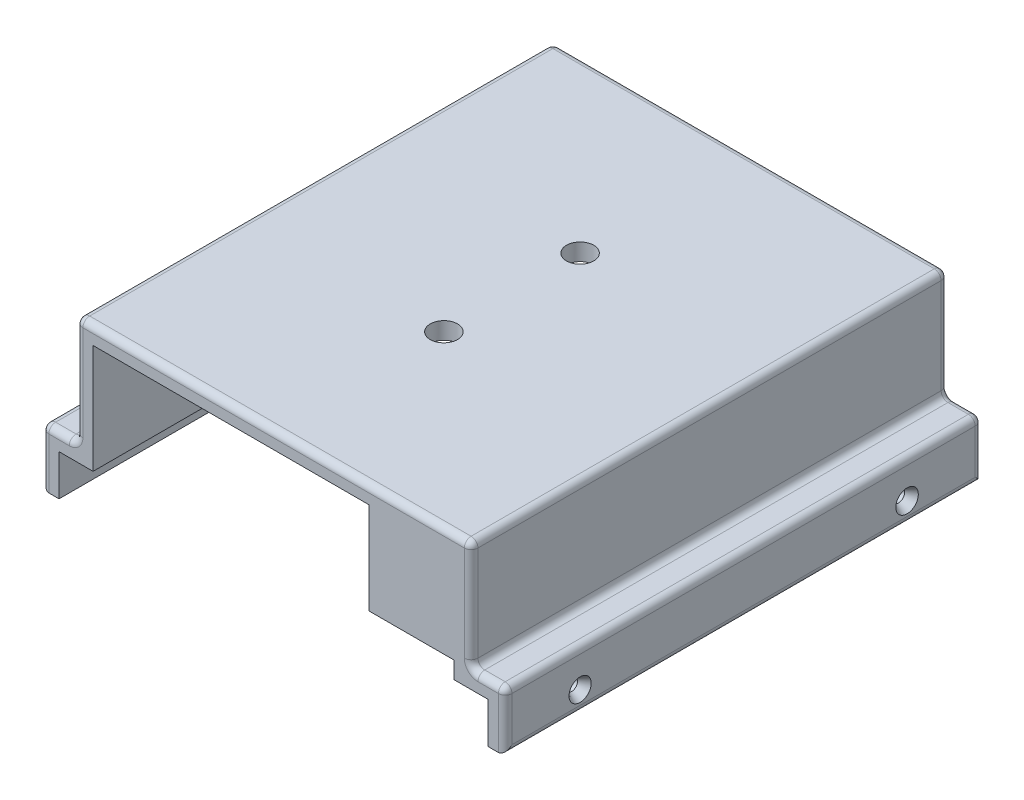
SolidWorks part; units mm, degrees
ref_plane "Front Plane" through (0, 0, 0) normal (0, 0, 1) x (1, 0, 0)
ref_plane "Top Plane" through (0, 0, 0) normal (0, 1, 0) x (1, 0, 0)
ref_plane "Right Plane" through (0, 0, 0) normal (1, 0, 0) x (0, 0, -1)
sketch "Sketch3" plane through (0, 0, 0) normal (0, 0, 1) x (1, 0, 0)
  line L0 (-58, 0) -> (58, 0)
  line L1 (58, 0) -> (58, -32)
  line L2 (58, -32) -> (68, -32)
  line L3 (68, -32) -> (68, -49)
  line L4 (68, -49) -> (63, -49)
  line L5 (63, -49) -> (63, -37)
  line L6 (63, -37) -> (53, -37)
  line L7 (53, -37) -> (53, -5)
  line L8 (53, -5) -> (-53, -5)
  line L10 (-53, -37) -> (-53, -5)
  line L11 (-63, -37) -> (-53, -37)
  line L12 (-63, -49) -> (-63, -37)
  line L13 (-68, -49) -> (-63, -49)
  line L14 (-68, -32) -> (-68, -49)
  line L15 (-58, -32) -> (-68, -32)
  line L16 (-58, 0) -> (-58, -32)
  point P0 (-58, -16)
  dimension "D1" = 5
  dimension "D2" = 32
  dimension "D3" = 5
  dimension "D4" = 5
  dimension "D5" = 5
  dimension "D6" = 5
  dimension "D7" = 10
  dimension "D8" = 12
  dimension "D10" = 5
  dimension "D12" = 32
  dimension "D13" = 32
  dimension "D14" = 116
  dimension "D15" = 106
  dimension "D16" = 10
  dimension "D17" = 12
extrude "Boss-Extrude1" add sketch "Sketch3" against normal blind 140
sketch "Sketch4" plane through (0, 0, 0) normal (0, 0, 1) x (1, 0, 0)
  line L0 (28, -5) -> (28, -32)
  line L1 (-53, -5) -> (53, -5) construction
  line L2 (28, -32) -> (53, -32)
  line L3 (53, -5) -> (53, -37) construction
  line L4 (53, -32) -> (53, -5)
  line L5 (53, -5) -> (28, -5)
  dimension "D1" = 27
  dimension "D2" = 25
extrude "Boss-Extrude2" add sketch "Sketch4" against normal blind 5
sketch "Sketch5" plane through (0, 0, -140) normal (0, 0, -1) x (-1, 0, 0)
  line L0 (53, -5) -> (-53, -5) construction
  line L1 (28, -5) -> (28, -32)
  line L2 (28, -32) -> (53, -32)
  line L3 (53, -32) -> (53, -5)
  line L4 (53, -5) -> (28, -5)
  dimension "D1" = 27
  dimension "D2" = 25
extrude "Boss-Extrude3" add sketch "Sketch5" against normal blind 5
fillet "Fillet1" radius 2 22 edges at (-68, -49, -70) (-68, -40.5, -140) (-68, -40.5, 0) (-68, -32, -70) (-63, -32, -140) (-63, -32, 0) (-58, -32, -70) (-58, -16, -140) (-58, -16, 0) (68, -40.5, -140) (68, -49, -70) (68, -40.5, 0) (63, -32, -140) (68, -32, -70) (63, -32, 0) (58, -16, -140) (58, -32, -70) (58, -16, 0) (-58, 0, -70) (0, 0, -140) (58, 0, -70) (0, 0, 0)
sketch "Sketch6" plane through (68, 0, 0) normal (1, 0, 0) x (0, 0, -1)
  line L0 (2, -34) -> (2, -47) construction
  line L1 (138, -47) -> (138, -34) construction
  line L2 (2, -47) -> (138, -47) construction
  circle A0 centre (22, -43) radius 1.75
  circle A1 centre (118, -43) radius 1.8
  point P8 (0, 0)
  point P9 (0, 0)
  point P12 (0, 0)
  dimension "D1" = 3.5
  dimension "D2" = 3.6
  dimension "D3" = 20
  dimension "D4" = 20
  dimension "D5" = 4
  dimension "D6" = 4
extrude "Cut-Extrude1" cut sketch "Sketch6" against normal through all
chamfer "Chamfer1" distance 1.5 distance2 2.5 2 edges at (68, -43, -119.8) (68, -43, -23.75)
chamfer "Chamfer2" distance 2.5 distance2 1.5 2 edges at (-68, -43, -23.75) (-68, -43, -119.8)
sketch "Sketch8" plane through (0, 0, 0) normal (0, 1, 0) x (1, 0, 0)
  line L0 (58, 2) -> (58, 138) construction
  circle A0 centre (0, 90) radius 4
  circle A1 centre (0, 50) radius 4
  point P0 (0, 70)
  point P3 (58, 70)
  dimension "D1" = 8
  dimension "D2" = 8
  dimension "D3" = 20
  dimension "D4" = 20
extrude "Cut-Extrude2" cut sketch "Sketch8" against normal through all
